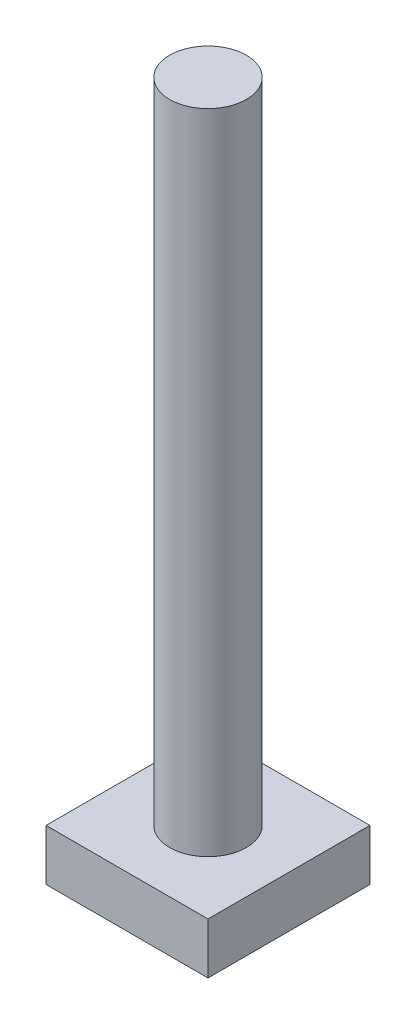
SolidWorks part; units mm, degrees
ref_plane "Front Plane" through (0, 0, 0) normal (0, 0, 1) x (1, 0, 0)
ref_plane "Top Plane" through (0, 0, 0) normal (0, 1, 0) x (1, 0, 0)
ref_plane "Right Plane" through (0, 0, 0) normal (1, 0, 0) x (0, 0, -1)
sketch "Sketch1" plane through (0, 0, 0) normal (0, 1, 0) x (1, 0, 0)
  line L1 (9.5, -9.5) -> (-9.5, -9.5)
  line L2 (9.5, -9.5) -> (9.5, 9.5)
  line L3 (9.5, 9.5) -> (-9.5, 9.5)
  line L4 (-9.5, -9.5) -> (-9.5, 9.5)
  line L5 (9.5, -9.5) -> (-9.5, 9.5) construction
  line L6 (9.5, 9.5) -> (-9.5, -9.5) construction
  point P0 (0, 0)
  dimension "D1" = 19
extrude "Boss-Extrude1" add sketch "Sketch1" along normal blind 6
sketch "Sketch2" plane through (0, 6, 0) normal (0, 1, 0) x (1, 0, 0)
  circle A0 centre (0, 0) radius 4.5
  dimension "D1" = 9
extrude "Boss-Extrude2" add sketch "Sketch2" along normal blind 76
